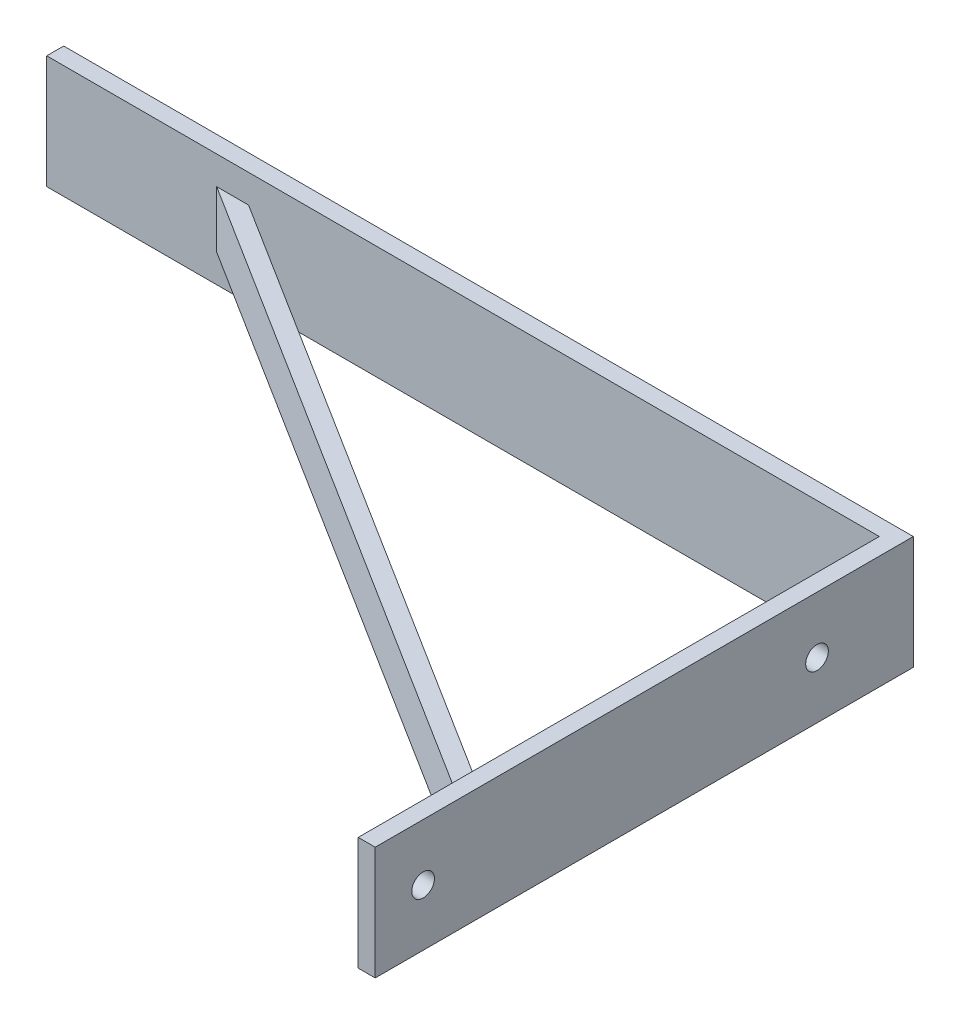
SolidWorks part; units mm, degrees
ref_plane "Front Plane" through (0, 0, 0) normal (0, 0, 1) x (1, 0, 0)
ref_plane "Top Plane" through (0, 0, 0) normal (0, 1, 0) x (1, 0, 0)
ref_plane "Right Plane" through (0, 0, 0) normal (1, 0, 0) x (0, 0, -1)
sketch "Croquis1" plane through (0, 0, 0) normal (0, 1, 0) x (1, 0, 0)
  line L0 (-147, 3) -> (-147, 0)
  line L1 (-147, 0) -> (0, 0)
  line L2 (0, 0) -> (0, -92)
  line L3 (0, -92) -> (3, -92)
  line L4 (3, -92) -> (3, 3)
  line L5 (3, 3) -> (-147, 3)
  line L6 (-117, 0) -> (0, -73.5434)
  line L7 (-111.3628, 0) -> (0, -70)
  dimension "D1" = 150
  dimension "D2" = 95
  dimension "D3" = 147
  dimension "D4" = 3
  dimension "D5" = 3
  dimension "D6" = 70
  dimension "D7" = 30
extrude "Saliente-Extruir1" add sketch "Croquis1" along normal blind 20 contours L4 L5 L0 L1 L2 L3 | L7 L1 L6 L2
sketch "Croquis2" plane through (0, 0, 0) normal (-1, 0, 0) x (0, 0, 1)
  line L0 (0, 20) -> (0, 0) construction
  line L1 (73.5434, 20) -> (73.5434, 0) construction
  line L3 (0, 0) -> (70, 0) construction
  circle A0 centre (83.5434, 10) radius 2
  circle A1 centre (14, 10) radius 2
  dimension "D1" = 4
  dimension "D2" = 4
  dimension "D3" = 14
  dimension "D4" = 10
  dimension "D5" = 10
  dimension "D6" = 10
extrude "Cortar-Extruir1" cut sketch "Croquis2" against normal blind 20
sketch "Croquis3" plane through (0, 0, 0) normal (0, -1, 0) x (1, 0, 0)
  line L0 (0, 70) -> (0, 73.5434)
  line L1 (0, 73.5434) -> (-117, 0)
  line L2 (-117, 0) -> (-111.3628, 0)
  line L3 (-111.3628, 0) -> (0, 70)
extrude "Cortar-Extruir2" cut sketch "Croquis3" against normal blind 5
sketch "Croquis4" plane through (0, 20, 0) normal (0, 1, 0) x (1, 0, 0)
  line L0 (0, -73.5434) -> (0, -70)
  line L1 (0, -70) -> (-111.3628, 0)
  line L2 (-111.3628, 0) -> (-117, 0)
  line L3 (-117, 0) -> (0, -73.5434)
extrude "Cortar-Extruir3" cut sketch "Croquis4" against normal blind 5
